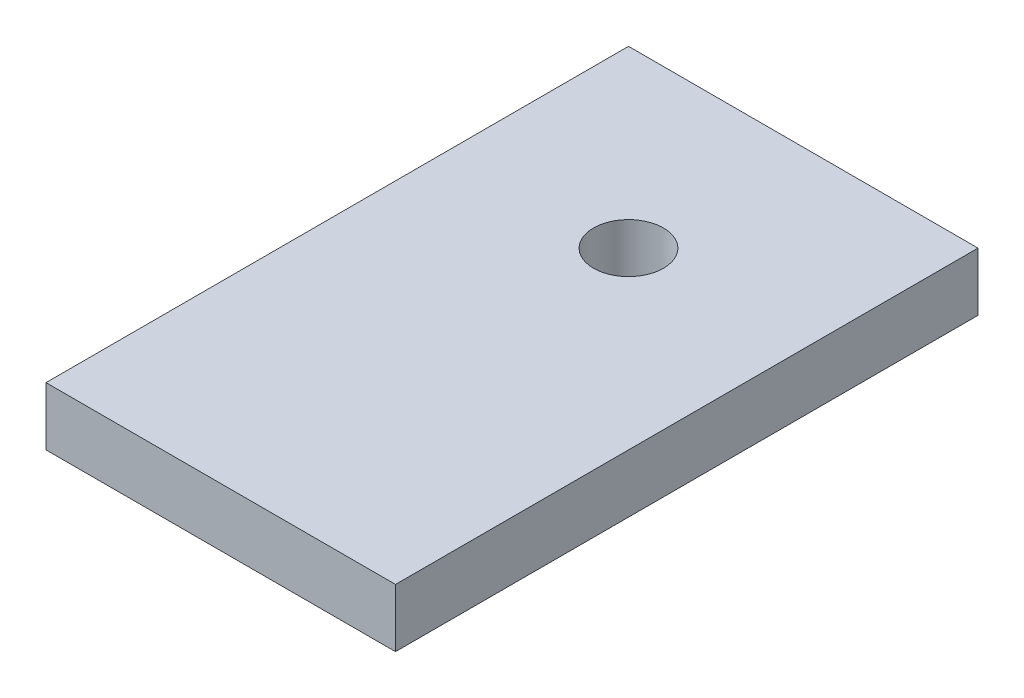
SolidWorks part; units mm, degrees
ref_plane "Front Plane" through (0, 0, 0) normal (0, 0, 1) x (1, 0, 0)
ref_plane "Top Plane" through (0, 0, 0) normal (0, 1, 0) x (1, 0, 0)
ref_plane "Right Plane" through (0, 0, 0) normal (1, 0, 0) x (0, 0, -1)
sketch "Sketch1" plane through (0, 0, 0) normal (0, 1, 0) x (1, 0, 0)
  line L1 (15, -25) -> (-15, -25)
  line L2 (15, -25) -> (15, 25)
  line L3 (15, 25) -> (-15, 25)
  line L4 (-15, -25) -> (-15, 25)
  line L5 (15, -25) -> (-15, 25) construction
  line L6 (15, 25) -> (-15, -25) construction
  point P0 (0, 0)
  dimension "D1" = 50
  dimension "D2" = 30
extrude "Boss-Extrude1" add sketch "Sketch1" along normal blind 5
sketch "Sketch2" plane through (0, 5, 0) normal (0, 1, 0) x (1, 0, 0)
  line L0 (15, 25) -> (-15, 25) construction
  circle A0 centre (0, 10) radius 3
  dimension "D1" = 15
extrude "Cut-Extrude1" cut sketch "Sketch2" against normal blind 5
